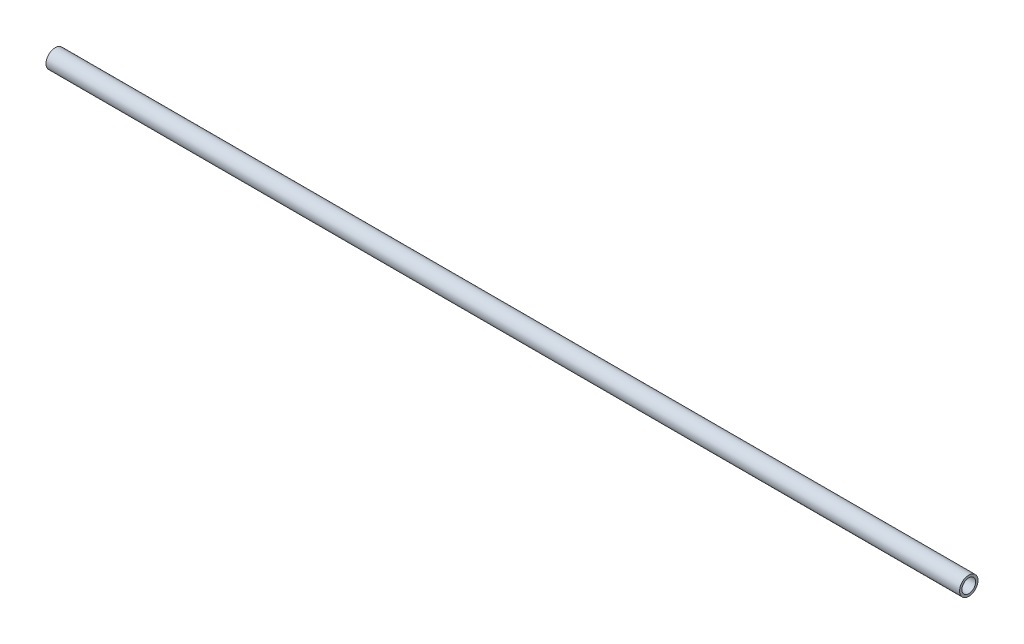
SolidWorks part; units mm, degrees
ref_plane "Front Plane" through (0, 0, 0) normal (0, 0, 1) x (1, 0, 0)
ref_plane "Top Plane" through (0, 0, 0) normal (0, 1, 0) x (1, 0, 0)
ref_plane "Right Plane" through (0, 0, 0) normal (1, 0, 0) x (0, 0, -1)
sketch "Sketch1" plane through (0, 0, 0) normal (1, 0, 0) x (0, 0, -1)
  circle A0 centre (0, 0) radius 4.7625
  circle A1 centre (0, 0) radius 6.4135
  dimension "D2" = 9.525
  dimension "D1" = 1.651
extrude "Boss-Extrude1" add sketch "Sketch1" along normal blind 635
